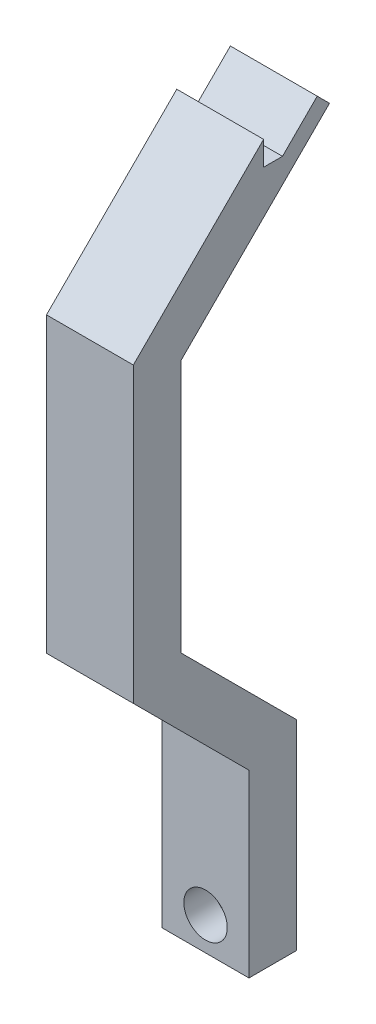
SolidWorks part; units mm, degrees
ref_plane "Piano frontale" through (0, 0, 0) normal (0, 0, 1) x (1, 0, 0)
ref_plane "Piano superiore" through (0, 0, 0) normal (0, 1, 0) x (1, 0, 0)
ref_plane "Piano destro" through (0, 0, 0) normal (1, 0, 0) x (0, 0, -1)
sketch "Schizzo1" plane through (0, 0, 0) normal (1, 0, 0) x (0, 0, -1)
  line L0 (-21.1885, 88.9449) -> (-26.6885, 88.9449)
  line L1 (-26.6885, 88.9449) -> (-26.6885, 109.6667)
  line L2 (-26.6885, 109.6667) -> (-40, 122.9783)
  line L3 (-40, 122.9783) -> (-40, 156.7231)
  line L4 (-40, 156.7231) -> (-25, 171.7231)
  line L5 (-25, 171.7231) -> (-25, 168.9449)
  line L6 (-25, 168.9449) -> (-22.8284, 168.9449)
  line L7 (-22.8284, 168.9449) -> (-18.8284, 172.9449)
  line L8 (-18.8284, 172.9449) -> (-17.4142, 171.5307)
  line L9 (-17.4142, 171.5307) -> (-34.5, 154.4449)
  line L10 (-34.5, 154.4449) -> (-34.5, 125.2564)
  line L11 (-34.5, 125.2564) -> (-21.1885, 111.9449)
  line L12 (-21.1885, 111.9449) -> (-21.1885, 88.9449)
  line L13 (-25, 168.9449) -> (-20, 168.9449) construction
  line L14 (-21.1885, 89.5249) -> (-21.1885, 111.9449) construction
  line L15 (0, 59.0622) -> (0, 153.8359) construction
  dimension "D1" = 5.5
  dimension "D2" = 5.5
  dimension "D3" = 5.5
  dimension "D4" = 5.5
  dimension "D5" = 5
  dimension "D6" = 4
  dimension "D7" = 2
  dimension "D8" = 23
  dimension "D9" = 80
  dimension "D10" = 15
  dimension "D11" = 25
extrude "Estrusione-Estrusione1" add sketch "Schizzo1" along normal mid plane 10
sketch "Schizzo2" plane through (0, 0, 26.6885) normal (0, 0, 1) x (1, 0, 0)
  circle A0 centre (0, 92.7235) radius 1.625
  dimension "D1" = 3.25
extrude "Taglio-Estrusione1" cut sketch "Schizzo2" against normal through all
sketch "Schizzo3" plane through (0, 0, 26.6885) normal (0, 0, 1) x (1, 0, 0)
  circle A0 centre (0, 92.7235) radius 2.5
extrude "Taglio-Estrusione2" cut sketch "Schizzo3" against normal blind 3.5
